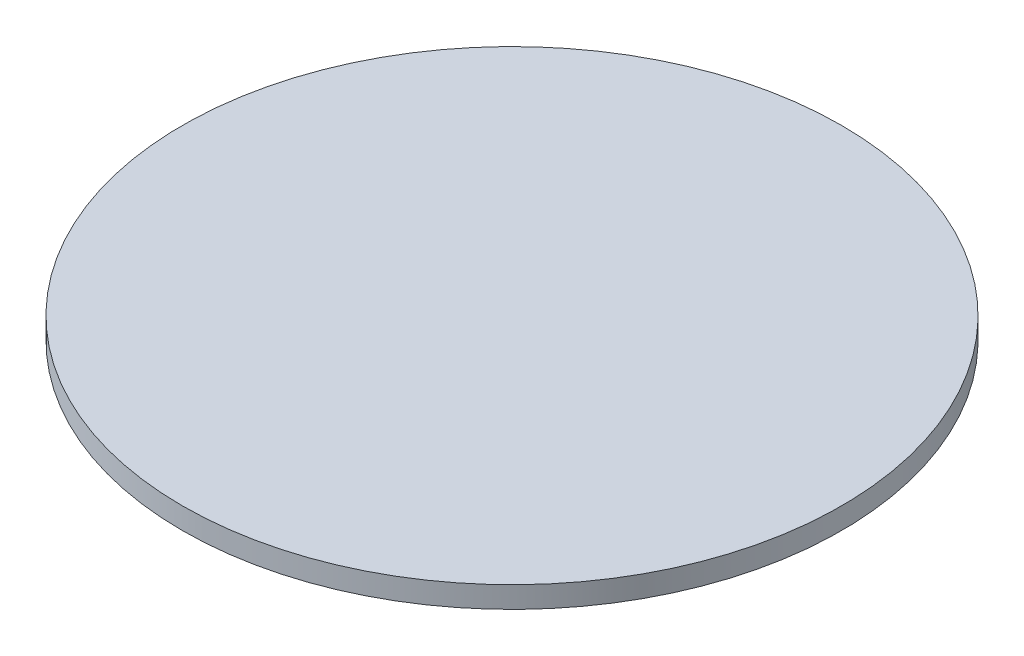
SolidWorks part; units mm, degrees
ref_plane "Front Plane" through (0, 0, 0) normal (0, 0, 1) x (1, 0, 0)
ref_plane "Top Plane" through (0, 0, 0) normal (0, 1, 0) x (1, 0, 0)
ref_plane "Right Plane" through (0, 0, 0) normal (1, 0, 0) x (0, 0, -1)
sketch "Sketch2" plane through (0, 0, 0) normal (0, 1, 0) x (1, 0, 0)
  circle A0 centre (0, 0) radius 152.4
extrude "Boss-Extrude1" add sketch "Sketch2" along normal blind 9.906
